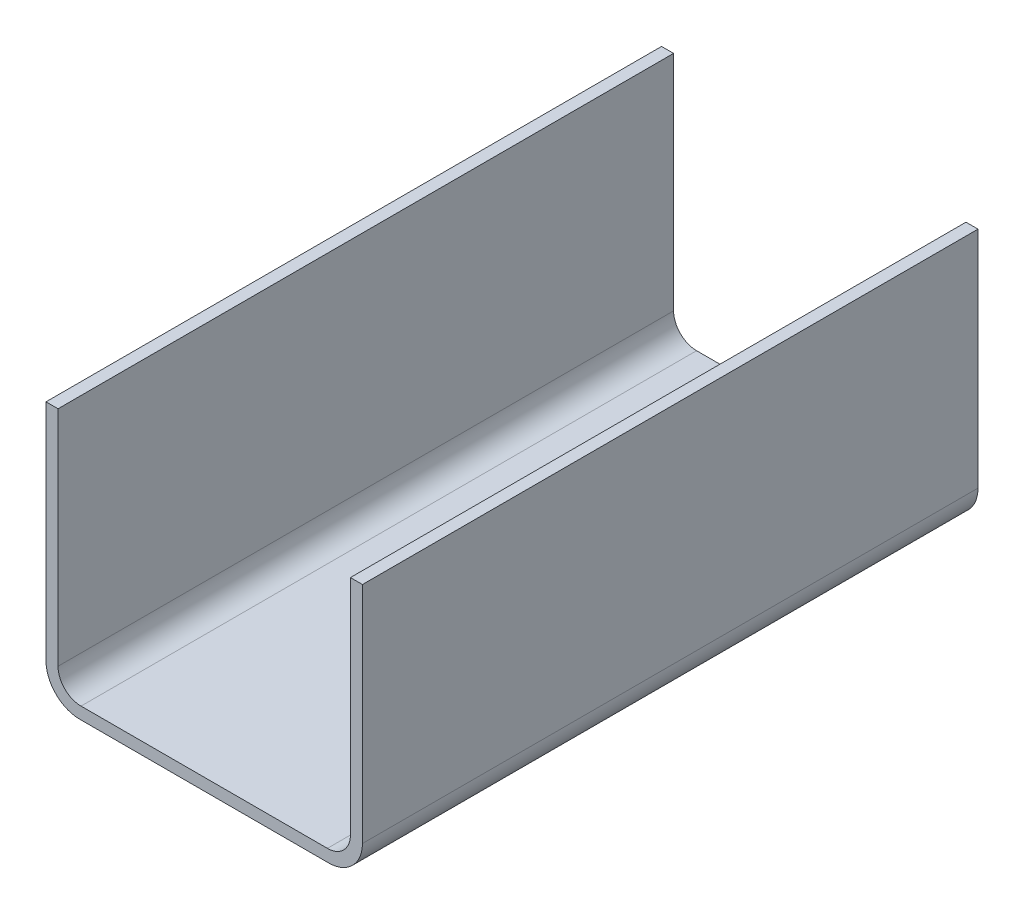
SolidWorks part; units mm, degrees
ref_plane "Front Plane" through (0, 0, 0) normal (0, 0, 1) x (1, 0, 0)
ref_plane "Top Plane" through (0, 0, 0) normal (0, 1, 0) x (1, 0, 0)
ref_plane "Right Plane" through (0, 0, 0) normal (1, 0, 0) x (0, 0, -1)
sketch "Sketch1" plane through (0, 0, 0) normal (0, 0, 1) x (1, 0, 0)
  line L0 (-95.35, 84.15) -> (-95.35, -76.3)
  line L1 (-103.2, -84.15) -> (103.2, -84.15)
  line L2 (-103.2, -84.15) -> (-103.2, 84.15)
  line L3 (-103.2, 84.15) -> (-95.35, 84.15)
  line L4 (103.2, -84.15) -> (103.2, 84.15)
  line L5 (-103.2, -84.15) -> (103.2, 84.15) construction
  line L6 (-103.2, 84.15) -> (103.2, -84.15) construction
  line L7 (-95.35, -76.3) -> (95.35, -76.3)
  line L8 (95.35, -76.3) -> (95.35, 84.15)
  line L9 (0, 185.2788) -> (0, -158.0083) construction
  line L10 (95.35, 84.15) -> (103.2, 84.15)
  point P0 (0, 0)
  dimension "D1" = 206.4
  dimension "D2" = 190.7
  dimension "D3" = 95.35
  dimension "D4" = 95.35
  dimension "D5" = 7.85
  dimension "D6" = 168.3
extrude "Boss-Extrude1" add sketch "Sketch1" along normal blind 401.5
fillet "Fillet2" radius 15 2 edges at (95.35, -76.3, 200.75) (-95.35, -76.3, 200.75)
fillet "Fillet4" radius 22 2 edges at (-103.2, -84.15, 200.75) (103.2, -84.15, 200.75)
sketch "Sketch2" plane through (0, 84.15, 0) normal (0, 1, 0) x (1, 0, 0)
  line L0 (0, 80.2447) -> (0, -460.9303) construction
